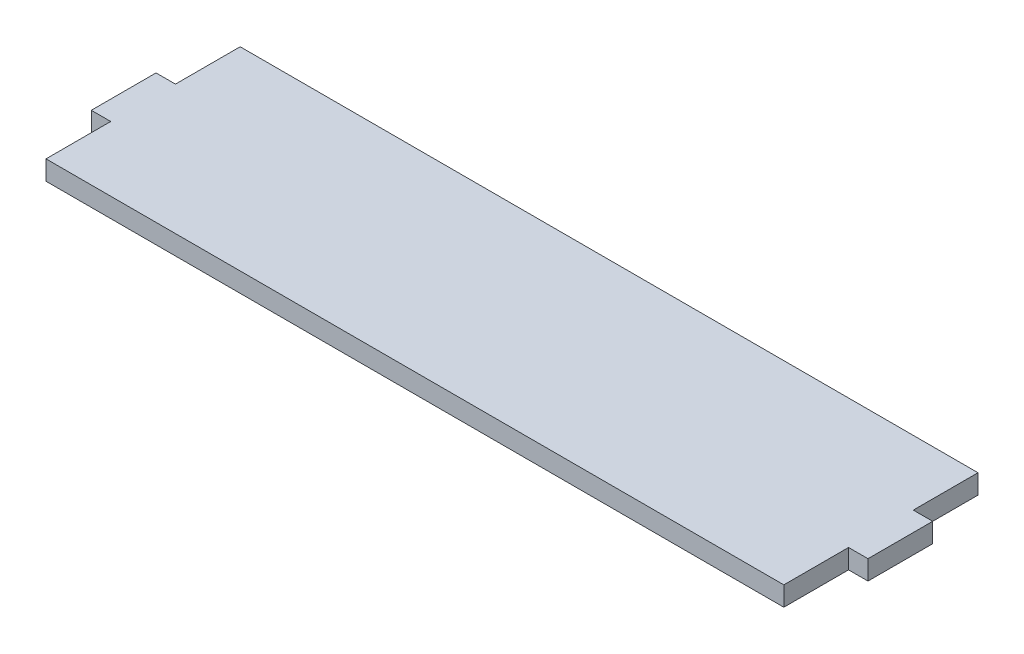
SolidWorks part; units mm, degrees
ref_plane "Alzado" through (0, 0, 0) normal (0, 0, 1) x (1, 0, 0)
ref_plane "Planta" through (0, 0, 0) normal (0, 1, 0) x (1, 0, 0)
ref_plane "Vista lateral" through (0, 0, 0) normal (1, 0, 0) x (0, 0, -1)
sketch "Croquis1" plane through (0, 0, 0) normal (0, 1, 0) x (1, 0, 0)
  line L0 (-57, 5) -> (-60, 5)
  line L1 (57, -15) -> (-57, -15)
  line L2 (57, -15) -> (57, -5)
  line L3 (57, 15) -> (-57, 15)
  line L4 (-57, -15) -> (-57, -5)
  line L5 (57, -15) -> (-57, 15) construction
  line L6 (57, 15) -> (-57, -15) construction
  line L7 (-60, 5) -> (-60, -5)
  line L8 (-60, -5) -> (-57, -5)
  line L9 (0, 0) -> (0, -61.5566) construction
  line L10 (60, -5) -> (57, -5)
  line L11 (60, 5) -> (60, -5)
  line L12 (57, 5) -> (60, 5)
  line L13 (0, 0) -> (113.1674, 0) construction
  line L14 (57, 5) -> (57, 15)
  line L15 (-57, 5) -> (-57, 15)
  point P0 (0, 0)
  dimension "D1" = 120
  dimension "D2" = 3
  dimension "D3" = 10
  dimension "D4" = 30
extrude "Saliente-Extruir1" add sketch "Croquis1" along normal blind 3
